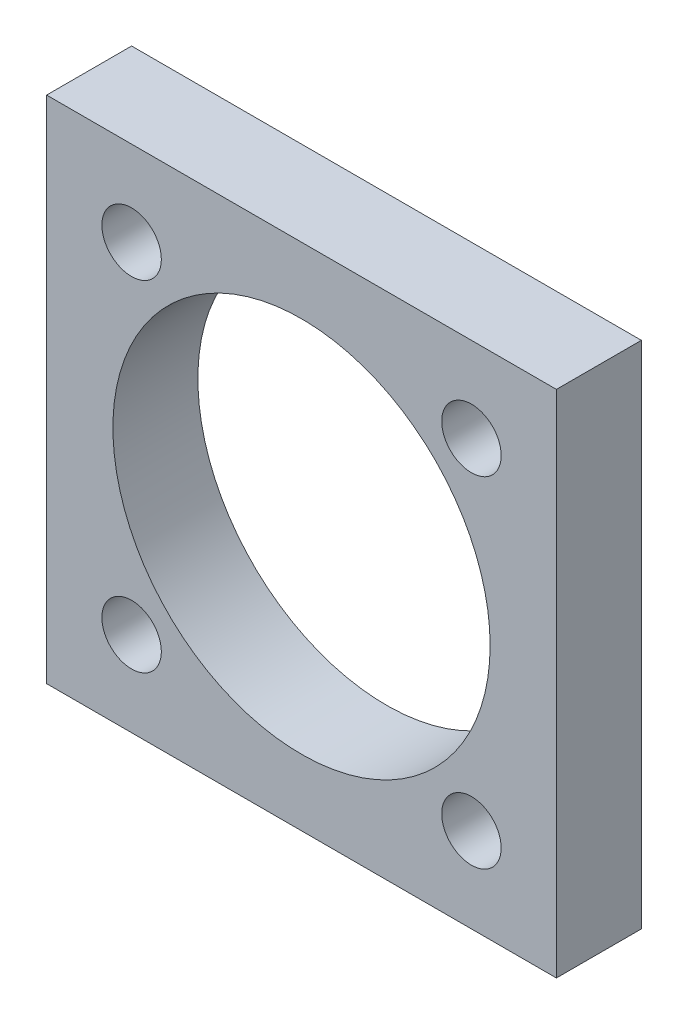
SolidWorks part; units mm, degrees
material "Lega 1060"
ref_plane "Piano frontale" through (0, 0, 0) normal (0, 0, 1) x (1, 0, 0)
ref_plane "Piano superiore" through (0, 0, 0) normal (0, 1, 0) x (1, 0, 0)
ref_plane "Piano destro" through (0, 0, 0) normal (1, 0, 0) x (0, 0, -1)
sketch "Schizzo1" plane through (0, 0, 0) normal (0, 0, 1) x (1, 0, 0)
  line L0 (0, 9.2511) -> (0, 0) construction
  line L1 (15, -15) -> (-15, -15)
  line L2 (15, -15) -> (15, 15)
  line L3 (15, 15) -> (-15, 15)
  line L4 (-15, -15) -> (-15, 15)
  line L5 (0, 0) -> (6.1449, 0) construction
  line L6 (0, 0) -> (-15, 15) construction
  circle A0 centre (-10, 10) radius 1.75
  circle A1 centre (10, 10) radius 1.75
  circle A2 centre (10, -10) radius 1.75
  circle A3 centre (-10, -10) radius 1.75
  circle A4 centre (0, 0) radius 11.1
  point P20 (0, 0)
  dimension "D3" = 3.5
  dimension "D6" = 22.2
  dimension "D1" = 30
  dimension "D2" = 30
  dimension "D4" = 5
  dimension "D5" = 4
extrude "Estrusione-Estrusione1" add sketch "Schizzo1" along normal blind 5
